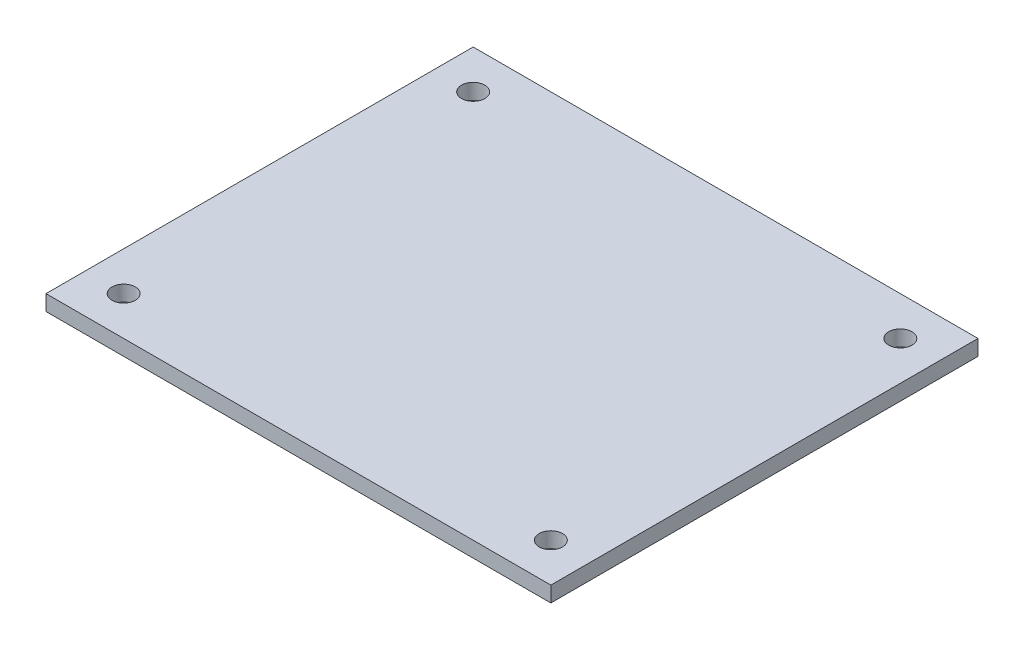
SolidWorks part; units mm, degrees
ref_plane "Alzado" through (0, 0, 0) normal (0, 0, 1) x (1, 0, 0)
ref_plane "Planta" through (0, 0, 0) normal (0, 1, 0) x (1, 0, 0)
ref_plane "Vista lateral" through (0, 0, 0) normal (1, 0, 0) x (0, 0, -1)
sketch "Croquis2" plane through (0, 0, 0) normal (0, 1, 0) x (1, 0, 0)
  line L1 (-32.5, -27.5) -> (32.5, -27.5)
  line L2 (-32.5, -27.5) -> (-32.5, 27.5)
  line L3 (-32.5, 27.5) -> (32.5, 27.5)
  line L4 (32.5, -27.5) -> (32.5, 27.5)
  line L5 (-32.5, -27.5) -> (32.5, 27.5) construction
  line L6 (-32.5, 27.5) -> (32.5, -27.5) construction
  point P0 (0, 0)
extrude "Saliente-Extruir1" add sketch "Croquis2" along normal blind 2
sketch "Croquis3" plane through (0, 2, 0) normal (0, 1, 0) x (1, 0, 0)
  line L0 (-32.5, 27.5) -> (-32.5, 22.5) construction
  line L1 (-32.5, 27.5) -> (-32.5, -27.5) construction
  line L2 (-32.5, 22.5) -> (-27.5, 22.5) construction
  line L3 (32.5, 24) -> (27.5, 24) construction
  line L4 (32.5, -27.5) -> (32.5, 27.5) construction
  line L5 (27.5, 24) -> (27.5, 22.5) construction
  line L6 (27.5, -27.5) -> (27.5, -22.5) construction
  line L7 (-32.5, -27.5) -> (32.5, -27.5) construction
  line L8 (27.5, -22.5) -> (32.5, -22.5) construction
  line L9 (-32.5, -24) -> (-27.5, -24) construction
  line L10 (-27.5, -24) -> (-27.5, -27.5) construction
  line L11 (-27.5, -27.5) -> (-27.5, -22.5) construction
  circle A0 centre (-27.5, 22.5) radius 1.5
  circle A1 centre (27.5, 22.5) radius 1.5
  circle A2 centre (27.5, -22.5) radius 1.5
  circle A3 centre (-27.5, -22.5) radius 1.5
extrude "Cortar-Extruir1" cut sketch "Croquis3" against normal through all
